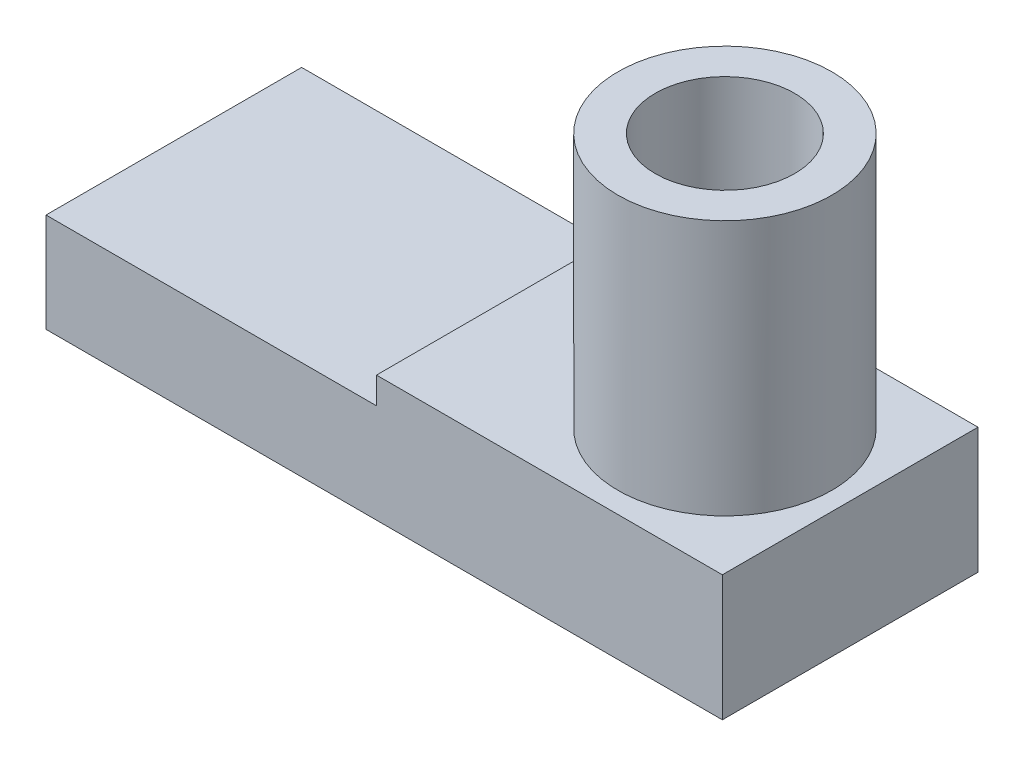
SolidWorks part; units mm, degrees
ref_plane "Přední rovina" through (0, 0, 0) normal (0, 0, 1) x (1, 0, 0)
ref_plane "Horní rovina" through (0, 0, 0) normal (0, 1, 0) x (1, 0, 0)
ref_plane "Pravá rovina" through (0, 0, 0) normal (1, 0, 0) x (0, 0, -1)
sketch "Skica1" plane through (0, 0, 0) normal (0, 0, 1) x (1, 0, 0)
  line L0 (0, 0) -> (0, 23.2424)
  line L1 (0, 23.2424) -> (77.5618, 23.2424)
  line L4 (158.7399, 29.4886) -> (158.7399, 0)
  line L5 (158.7399, 0) -> (0, 0)
  line L6 (77.5618, 23.2424) -> (77.5618, 29.4886)
  line L7 (77.5618, 29.4886) -> (158.7399, 29.4886)
extrude "Přidat vysunutím1" add sketch "Skica1" along normal mid plane 60
sketch "Skica2" plane through (0, 29.4886, 0) normal (0, 1, 0) x (1, 0, 0)
  circle A0 centre (129.3401, 0) radius 16.3524
  circle A1 centre (129.3401, 0) radius 25.1044
extrude "Přidat vysunutím2" add sketch "Skica2" along normal blind 60
sketch "Skica3" plane through (0, 0, 0) normal (0, 0, 1) x (1, 0, 0)
  line L0 (104.2358, 89.4886) -> (28.8925, 23.2424)
  line L1 (77.5618, 23.2424) -> (0, 23.2424) construction
  line L2 (104.2358, 89.4886) -> (104.2358, 29.4886) construction
  line L4 (154.4445, 89.4886) -> (104.2358, 89.4886) construction
  point P5 (104.2358, 63.8993)
  point P8 (104.2358, 89.4837)
  point P9 (104.2358, 90.01)
  point P10 (104.2358, 89.9144)
  point P11 (104.2358, 90.109)
